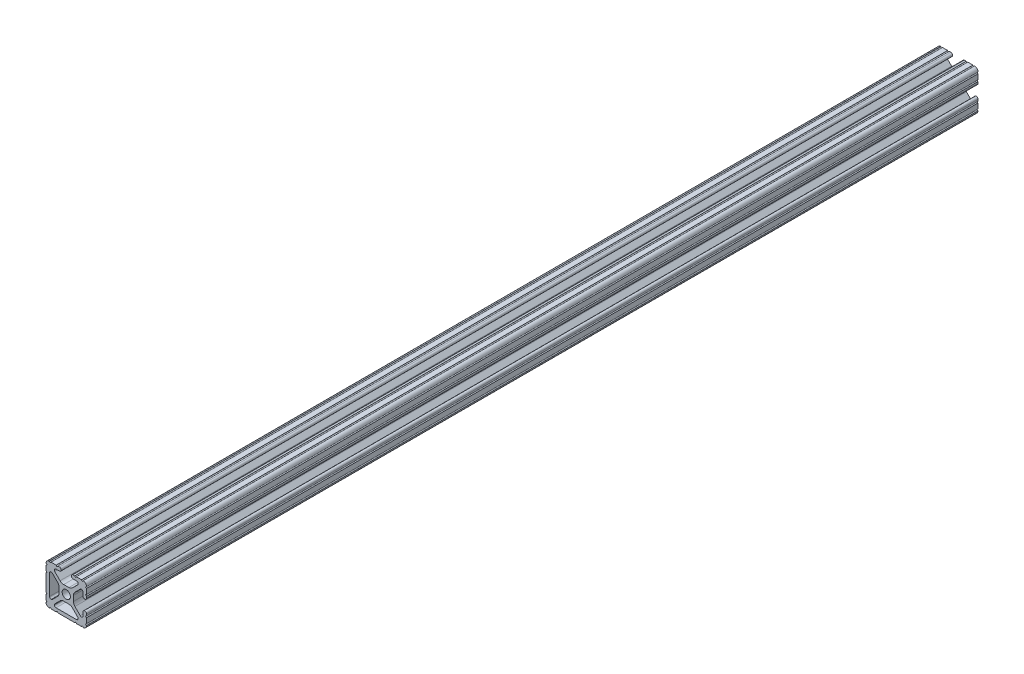
SolidWorks part; units mm, degrees
ref_plane "Front Plane" through (0, 0, 0) normal (0, 0, 1) x (1, 0, 0)
ref_plane "Top Plane" through (0, 0, 0) normal (0, 1, 0) x (1, 0, 0)
ref_plane "Right Plane" through (0, 0, 0) normal (1, 0, 0) x (0, 0, -1)
ref_plane "Plane1" through (0, 0, -558.8) normal (0, 0, -1) x (-1, 0, 0)
sketch "Sketch1" plane through (0, 0, -558.8) normal (0, 0, -1) x (-1, 0, 0)
  line L0 (12.7, -9.5504) -> (12.7, -6.3246)
  line L1 (12.7, -5.3086) -> (12.7, 5.3086)
  line L2 (12.7, 6.3246) -> (12.7, 9.5504)
  line L3 (9.5504, 12.7) -> (6.3246, 12.7)
  line L4 (5.3086, 12.7) -> (4.3023, 12.7)
  line L5 (4.3023, 10.4902) -> (6.4748, 10.4902)
  line L6 (7.1932, 8.7558) -> (3.8759, 5.4384)
  line L7 (1.6308, 4.5085) -> (-1.6308, 4.5085)
  line L8 (-3.8759, 5.4384) -> (-7.1932, 8.7558)
  line L9 (-6.4748, 10.4902) -> (-4.3023, 10.4902)
  line L10 (-4.3023, 12.7) -> (-5.3086, 12.7)
  line L11 (-6.3246, 12.7) -> (-9.5504, 12.7)
  line L12 (-12.7, 9.5504) -> (-12.7, 6.3246)
  line L13 (-12.7, 5.3086) -> (-12.7, 4.3023)
  line L14 (-10.4902, 4.3023) -> (-10.4902, 6.4748)
  line L15 (-8.7558, 7.1932) -> (-5.4384, 3.8759)
  line L16 (-4.5085, 1.6308) -> (-4.5085, -1.6308)
  line L17 (-5.4384, -3.8759) -> (-8.7558, -7.1932)
  line L18 (-10.4902, -6.4748) -> (-10.4902, -4.3023)
  line L19 (-12.7, -4.3023) -> (-12.7, -5.3086)
  line L20 (-12.7, -6.3246) -> (-12.7, -9.5504)
  line L21 (-9.5504, -12.7) -> (-6.3246, -12.7)
  line L22 (-5.3086, -12.7) -> (5.3086, -12.7)
  line L23 (6.3246, -12.7) -> (9.5504, -12.7)
  line L24 (3.8759, -5.4384) -> (7.1319, -8.6945)
  line L25 (6.4135, -10.4902) -> (-6.4135, -10.4902)
  line L26 (-7.1319, -8.6945) -> (-3.8759, -5.4384)
  line L27 (-1.6308, -4.5085) -> (1.6308, -4.5085)
  line L28 (10.4902, 6.4135) -> (10.4902, -6.4135)
  line L29 (8.6945, -7.1319) -> (5.4384, -3.8759)
  line L30 (4.5085, -1.6308) -> (4.5085, 1.6308)
  line L31 (5.4384, 3.8759) -> (8.6945, 7.1319)
  arc A0 (12.7, -10.5664) -> (12.7, -9.5504) centre (12.7, -10.0584) cw
  arc A1 (12.7, -6.3246) -> (12.7, -5.3086) centre (12.7, -5.8166) cw
  arc A2 (12.7, 5.3086) -> (12.7, 6.3246) centre (12.7, 5.8166) cw
  arc A3 (12.7, 9.5504) -> (12.7, 10.5664) centre (12.7, 10.0584) cw
  arc A4 (12.7, 10.5664) -> (10.5664, 12.7) centre (10.592, 10.592) ccw
  arc A5 (10.5664, 12.7) -> (9.5504, 12.7) centre (10.0584, 12.7) cw
  arc A6 (6.3246, 12.7) -> (5.3086, 12.7) centre (5.8166, 12.7) cw
  arc A7 (4.3023, 12.7) -> (4.3023, 10.4902) centre (4.3023, 11.5951) ccw
  arc A8 (6.4748, 10.4902) -> (7.1932, 8.7558) centre (6.4748, 9.4742) cw
  arc A9 (3.8759, 5.4384) -> (1.6308, 4.5085) centre (1.6308, 7.6835) cw
  arc A10 (-1.6308, 4.5085) -> (-3.8759, 5.4384) centre (-1.6308, 7.6835) cw
  arc A11 (-7.1932, 8.7558) -> (-6.4748, 10.4902) centre (-6.4748, 9.4742) cw
  arc A12 (-4.3023, 10.4902) -> (-4.3023, 12.7) centre (-4.3023, 11.5951) ccw
  arc A13 (-5.3086, 12.7) -> (-6.3246, 12.7) centre (-5.8166, 12.7) cw
  arc A14 (-9.5504, 12.7) -> (-10.5664, 12.7) centre (-10.0584, 12.7) cw
  arc A15 (-10.5664, 12.7) -> (-12.7, 10.5664) centre (-10.592, 10.592) ccw
  arc A16 (-12.7, 10.5664) -> (-12.7, 9.5504) centre (-12.7, 10.0584) cw
  arc A17 (-12.7, 6.3246) -> (-12.7, 5.3086) centre (-12.7, 5.8166) cw
  arc A18 (-12.7, 4.3023) -> (-10.4902, 4.3023) centre (-11.5951, 4.3023) ccw
  arc A19 (-10.4902, 6.4748) -> (-8.7558, 7.1932) centre (-9.4742, 6.4748) cw
  arc A20 (-5.4384, 3.8759) -> (-4.5085, 1.6308) centre (-7.6835, 1.6308) cw
  arc A21 (-4.5085, -1.6308) -> (-5.4384, -3.8759) centre (-7.6835, -1.6308) cw
  arc A22 (-8.7558, -7.1932) -> (-10.4902, -6.4748) centre (-9.4742, -6.4748) cw
  arc A23 (-10.4902, -4.3023) -> (-12.7, -4.3023) centre (-11.5951, -4.3023) ccw
  arc A24 (-12.7, -5.3086) -> (-12.7, -6.3246) centre (-12.7, -5.8166) cw
  arc A25 (-12.7, -9.5504) -> (-12.7, -10.5664) centre (-12.7, -10.0584) cw
  arc A26 (-12.7, -10.5664) -> (-10.5664, -12.7) centre (-10.592, -10.592) ccw
  arc A27 (-10.5664, -12.7) -> (-9.5504, -12.7) centre (-10.0584, -12.7) cw
  arc A28 (-6.3246, -12.7) -> (-5.3086, -12.7) centre (-5.8166, -12.7) cw
  arc A29 (5.3086, -12.7) -> (6.3246, -12.7) centre (5.8166, -12.7) cw
  arc A30 (9.5504, -12.7) -> (10.5664, -12.7) centre (10.0584, -12.7) cw
  arc A31 (10.5664, -12.7) -> (12.7, -10.5664) centre (10.592, -10.592) ccw
  circle A32 centre (0, 0) radius 2.6035
  arc A33 (7.1319, -8.6945) -> (7.4295, -9.4742) centre (6.2865, -9.4638) cw
  arc A34 (7.4295, -9.4742) -> (6.4135, -10.4902) centre (6.4135, -9.4742) cw
  arc A35 (-6.4135, -10.4902) -> (-7.4295, -9.4742) centre (-6.4135, -9.4742) cw
  arc A36 (-7.4295, -9.4742) -> (-7.1319, -8.6945) centre (-6.2865, -9.4638) cw
  arc A37 (-3.8759, -5.4384) -> (-1.6308, -4.5085) centre (-1.6308, -7.6835) cw
  arc A38 (1.6308, -4.5085) -> (3.8759, -5.4384) centre (1.6308, -7.6835) cw
  arc A39 (9.4742, 7.4295) -> (10.4902, 6.4135) centre (9.4742, 6.4135) cw
  arc A40 (10.4902, -6.4135) -> (9.4742, -7.4295) centre (9.4742, -6.4135) cw
  arc A41 (9.4742, -7.4295) -> (8.6945, -7.1319) centre (9.4638, -6.2865) cw
  arc A42 (5.4384, -3.8759) -> (4.5085, -1.6308) centre (7.6835, -1.6308) cw
  arc A43 (4.5085, 1.6308) -> (5.4384, 3.8759) centre (7.6835, 1.6308) cw
  arc A44 (8.6945, 7.1319) -> (9.4742, 7.4295) centre (9.4638, 6.2865) cw
extrude "Boss-Extrude1" add sketch "Sketch1" against normal blind 558.8
